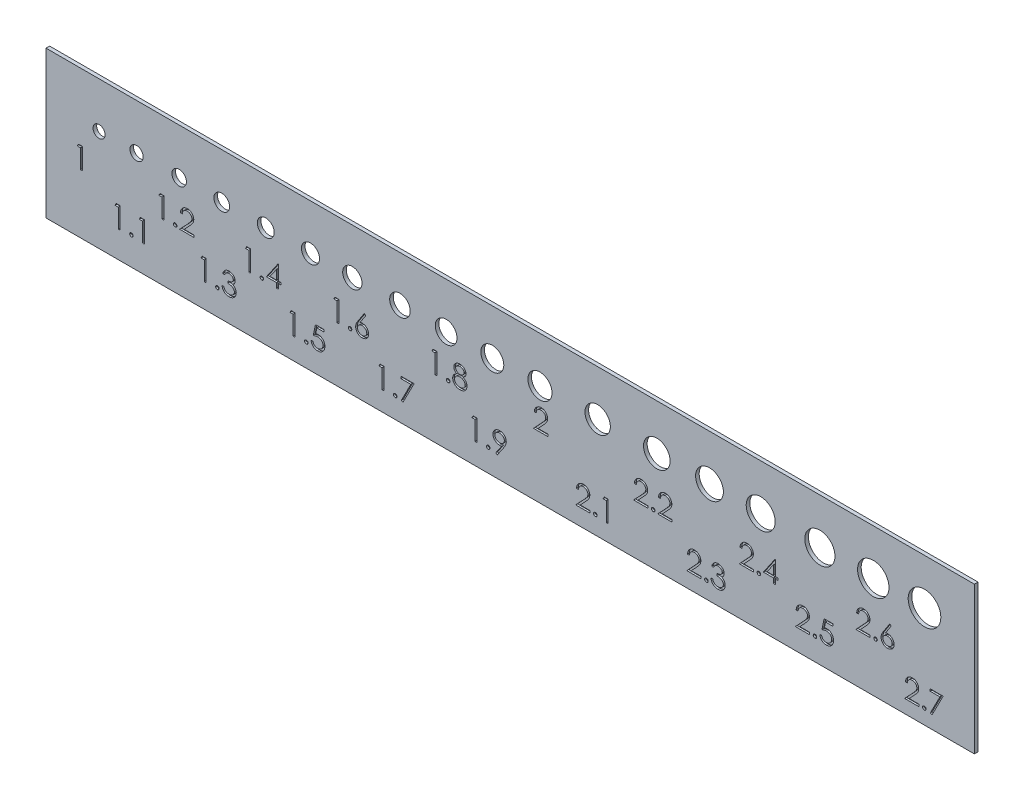
SolidWorks part; units mm, degrees
ref_plane "Plan de face" through (0, 0, 0) normal (0, 0, 1) x (1, 0, 0)
ref_plane "Plan de dessus" through (0, 0, 0) normal (0, 1, 0) x (1, 0, 0)
ref_plane "Plan de droite" through (0, 0, 0) normal (1, 0, 0) x (0, 0, -1)
sketch "Esquisse1" plane through (0, 0, 0) normal (0, 0, 1) x (1, 0, 0)
  line L0 (0, 27.1762) -> (153.6569, 27.1762) construction
  line L1 (0, 10.3828) -> (153.6569, 10.3828)
  line L2 (0, 10.3828) -> (0, 34.7252)
  line L3 (0, 34.7252) -> (153.6569, 34.7252)
  line L4 (153.6569, 10.3828) -> (153.6569, 34.7252)
  circle A0 centre (8.7856, 27.1762) radius 1
  circle A1 centre (14.9954, 27.1762) radius 1.1
  circle A2 centre (22.0412, 27.1762) radius 1.2
  circle A3 centre (29.087, 27.1762) radius 1.3
  circle A4 centre (36.3716, 27.1762) radius 1.4
  circle A5 centre (43.7757, 27.1762) radius 1.5
  circle A6 centre (50.702, 27.1762) radius 1.6
  circle A7 centre (58.5838, 27.1762) radius 1.7
  circle A8 centre (66.2267, 27.1762) radius 1.8
  circle A9 centre (73.8696, 27.1762) radius 1.9
  circle A10 centre (81.7513, 27.1762) radius 2
  circle A11 centre (91.3049, 27.1762) radius 2.1
  circle A12 centre (101.0974, 27.1762) radius 2.2
  circle A13 centre (109.815, 27.1762) radius 2.3
  circle A14 centre (118.2939, 27.1762) radius 2.4
  circle A15 centre (128.0863, 27.1762) radius 2.5
  circle A16 centre (136.9234, 27.1762) radius 2.6
  circle A17 centre (145.4022, 27.1762) radius 2.7
extrude "Boss.-Extru.1" add sketch "Esquisse1" along normal blind 0.6
sketch "Esquisse2" plane through (0, 0, 0.6) normal (0, 0, 1) x (1, 0, 0)
  text T0 "1"
  text T1 "1.1"
  text T2 "1.2"
  text T3 "1.3"
  text T4 "1.4"
  text T5 "1.5"
  text T6 "1.6"
  text T7 "1.7"
  text T8 "1.8"
  text T9 "1.9"
  text T10 "2"
  text T11 "2.1"
  text T12 "2.2"
  text T13 "2.3"
  text T14 "2.4"
  text T15 "2.5"
  text T16 "2.6"
  text T17 "2.7"
extrude "Enlèv. mat.-Extru.2" cut sketch "Esquisse2" against normal blind 0.3
